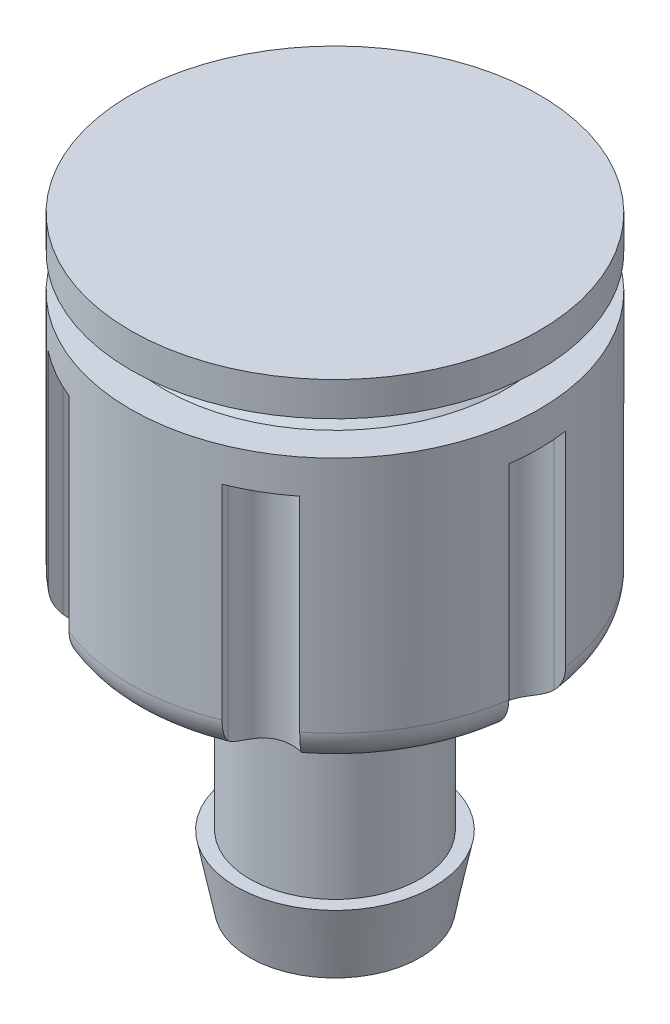
SolidWorks part; units mm, degrees
ref_plane "Front Plane" through (0, 0, 0) normal (0, 0, 1) x (1, 0, 0)
ref_plane "Top Plane" through (0, 0, 0) normal (0, 1, 0) x (1, 0, 0)
ref_plane "Right Plane" through (0, 0, 0) normal (1, 0, 0) x (0, 0, -1)
ref_plane "Plane1" through (0, 0, 0) normal (1, 0, 0) x (0, 0, -1)
sketch "Sketch1" plane through (0, 0, 0) normal (1, 0, 0) x (0, 0, -1)
  line L0 (0, 0) -> (6, 0)
  line L1 (6, 0) -> (6, -1)
  line L2 (6, -1) -> (5, -1)
  line L3 (5, -1) -> (4.5, -1.5)
  line L4 (4.5, -1.5) -> (5, -2)
  line L5 (5, -2) -> (6, -2)
  line L6 (6, -2) -> (6, -9)
  line L7 (5, -10) -> (3, -10)
  line L8 (3, -10) -> (2.5, -10.5)
  line L9 (2.5, -10.5) -> (2.5, -15.7)
  line L10 (2.5, -15.7) -> (2.8955, -15.7)
  line L11 (2.8955, -15.7) -> (2.5, -17.7)
  line L12 (2.5, -17.7) -> (1.5, -17.7)
  line L13 (1.5, -17.7) -> (1.5, -10)
  line L14 (1.5, -10) -> (0, -10)
  line L15 (0, -10) -> (0, 0)
  line L16 (0, -17.7) -> (0, 0) construction
  arc A0 (6, -9) -> (5, -10) centre (5, -9) cw
revolve "Revolve1" add sketch "Sketch1" angle 360 about L16
ref_plane "Plane2" through (0, -10, 0) normal (0, -1, 0) x (-1, 0, 0)
sketch "Sketch2" plane through (0, -10, 0) normal (0, -1, 0) x (-1, 0, 0)
  line L0 (-1, -14.9666) -> (-1, -9.9499)
  line L1 (-3.7461, -9.2718) -> (-2.1324, -5.2778)
  line L2 (-3.5045, -4.4856) -> (-6.1566, -7.8801)
  line L3 (-9.9027, -1.3917) -> (-5.6369, -0.7922)
  line L4 (-5.6369, 0.7922) -> (-9.9027, 1.3917)
  line L5 (-6.1566, 7.8801) -> (-3.5045, 4.4856)
  line L6 (-2.1324, 5.2778) -> (-3.7461, 9.2718)
  line L7 (3.7461, 9.2718) -> (2.1324, 5.2778)
  line L8 (3.5045, 4.4856) -> (6.1566, 7.8801)
  line L9 (9.9027, 1.3917) -> (5.6369, 0.7922)
  line L10 (5.6369, -0.7922) -> (9.9027, -1.3917)
  line L11 (6.1566, -7.8801) -> (3.5045, -4.4856)
  line L12 (2.1324, -5.2778) -> (3.7461, -9.2718)
  line L13 (0, -10) -> (0, -15)
  arc A0 (0, -15) -> (-1, -14.9666) centre (0, 0) ccw
  arc A1 (-1, -9.9499) -> (-3.7461, -9.2718) centre (0, 0) cw
  arc A2 (-2.1324, -5.2778) -> (-3.5045, -4.4856) centre (-2.8741, -4.9781) ccw
  arc A3 (-6.1566, -7.8801) -> (-9.9027, -1.3917) centre (0, 0) cw
  arc A4 (-5.6369, -0.7922) -> (-5.6369, 0.7922) centre (-5.7482, 0) ccw
  arc A5 (-9.9027, 1.3917) -> (-6.1566, 7.8801) centre (0, 0) cw
  arc A6 (-3.5045, 4.4856) -> (-2.1324, 5.2778) centre (-2.8741, 4.9781) ccw
  arc A7 (-3.7461, 9.2718) -> (3.7461, 9.2718) centre (0, 0) cw
  arc A8 (2.1324, 5.2778) -> (3.5045, 4.4856) centre (2.8741, 4.9781) ccw
  arc A9 (6.1566, 7.8801) -> (9.9027, 1.3917) centre (0, 0) cw
  arc A10 (5.6369, 0.7922) -> (5.6369, -0.7922) centre (5.7482, 0) ccw
  arc A11 (9.9027, -1.3917) -> (6.1566, -7.8801) centre (0, 0) cw
  arc A12 (3.5045, -4.4856) -> (2.1324, -5.2778) centre (2.8741, -4.9781) ccw
  arc A13 (3.7461, -9.2718) -> (0, -10) centre (0, 0) cw
extrude "Cut-Extrude1" cut sketch "Sketch2" against normal blind 7 and the other way blind 7
